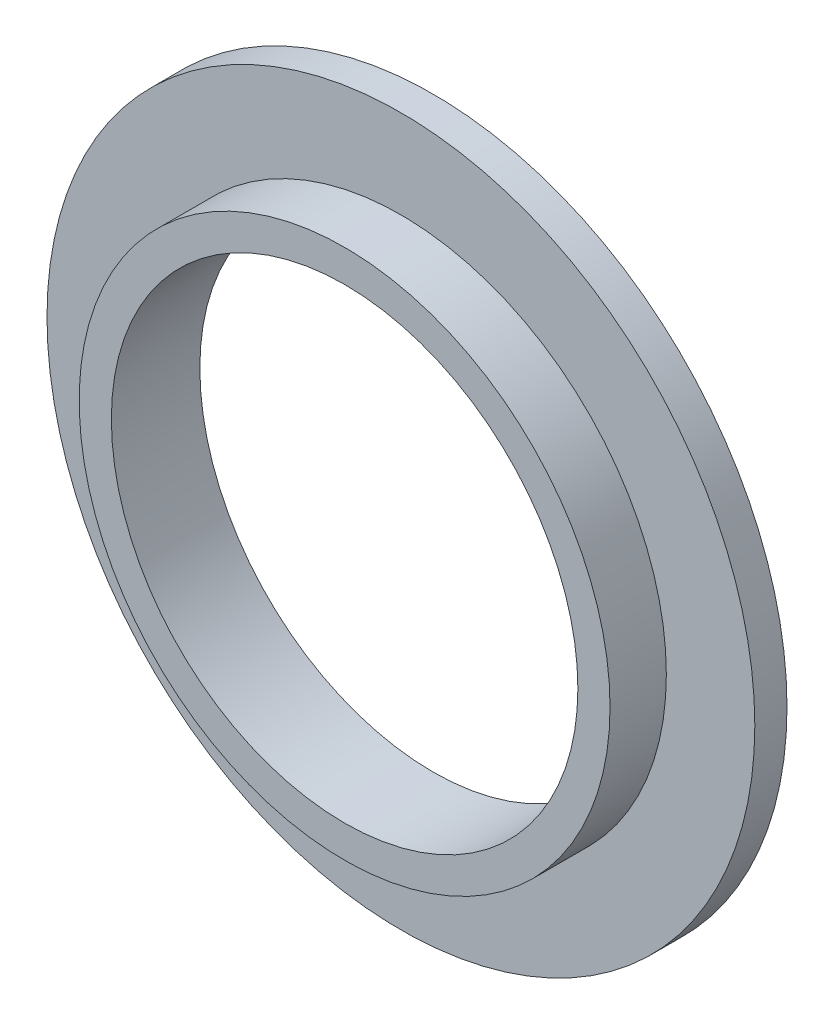
SolidWorks part; units mm, degrees
material "ABS"
ref_plane "Front Plane" through (0, 0, 0) normal (1, 0, 0) x (0, 1, 0)
ref_plane "Top Plane" through (0, 0, 0) normal (0, 0, 1) x (0, 1, 0)
ref_plane "Right Plane" through (0, 0, 0) normal (0, 1, 0) x (-1, 0, 0)
sketch "Sketch1" plane through (0, 0, 0) normal (0, 0, 1) x (0, 1, 0)
  circle A0 centre (0, 0) radius 44
  dimension "D1" = 88
extrude "Boss-Extrude1" add sketch "Sketch1" along normal blind 4
sketch "Sketch2" plane through (0, 0, 4) normal (0, 0, 1) x (1, 0, 0)
  circle A0 centre (0, 0) radius 33
  dimension "D1" = 66
extrude "Boss-Extrude2" add sketch "Sketch2" along normal blind 7
sketch "Sketch3" plane through (0, 0, 11) normal (0, 0, 1) x (1, 0, 0)
  circle A0 centre (0, 0) radius 29
  dimension "D1" = 58
extrude "Cut-Extrude1" cut sketch "Sketch3" against normal through all both and the other way through all
